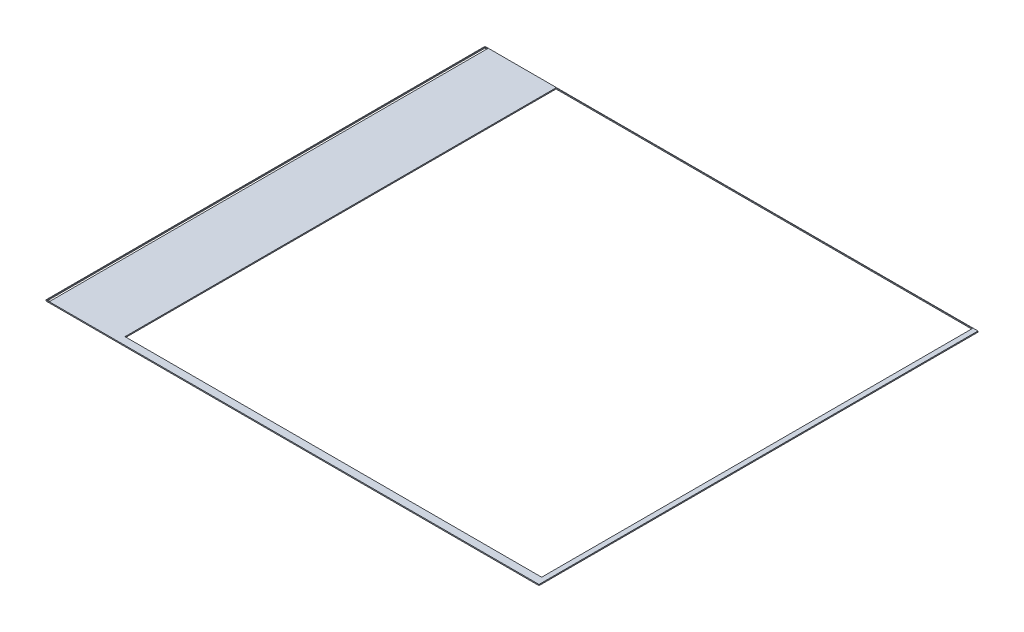
SolidWorks part; units mm, degrees
material "silicon D"
ref_plane "Front" through (0, 0, 0) normal (0, 0, 1) x (1, 0, 0)
ref_plane "Top" through (0, 0, 0) normal (0, 1, 0) x (1, 0, 0)
ref_plane "Right" through (0, 0, 0) normal (1, 0, 0) x (0, 0, -1)
sketch "Sketch1" plane through (0, 0, 0) normal (0, 1, 0) x (1, 0, 0)
  line L0 (11.355, 10.11) -> (-11.355, -10.11) construction
  line L1 (-11.355, 10.11) -> (11.355, 10.11) construction
  line L2 (-11.355, 10.11) -> (-11.355, -10.11) construction
  line L3 (-11.355, -10.11) -> (11.355, -10.11) construction
  line L4 (11.355, 10.11) -> (11.355, -10.11) construction
  line L5 (-11.365, 10.12) -> (11.365, 10.12)
  line L6 (11.365, 10.12) -> (11.365, -10.12)
  line L7 (-11.365, -10.12) -> (11.365, -10.12)
  line L8 (-11.365, 10.12) -> (-11.365, -10.12)
  point P4 (0, 0)
  dimension "D1" = 20.24
  dimension "D2" = 22.73
  dimension "D3" = 0.01
extrude "Extrude1" add sketch "Sketch1" along normal blind 0.05
sketch "Sketch2" plane through (0, 0, 0) normal (0, -1, 0) x (1, 0, 0)
  line L0 (-11.3446, 10.0882) -> (-11.2146, 10.0882) construction
  line L1 (-11.2146, -10.0968) -> (-11.3446, -10.0968) construction
  line L2 (-11.3446, -10.0968) -> (-11.3446, 10.0882) construction
  line L3 (-11.2146, 10.0882) -> (-11.2146, -10.0968) construction
  line L4 (-11.3446, 10.0882) -> (-11.2146, 10.0882)
  line L5 (-11.2146, -10.0968) -> (-11.3446, -10.0968)
  line L6 (-11.3446, -10.0968) -> (-11.3446, 10.0882)
  line L7 (-11.2146, 10.0882) -> (-11.2146, -10.0968)
extrude "Cut-Extrude1" cut sketch "Sketch2" against normal through all
sketch "Sketch3" plane through (0, 0, 0) normal (0, -1, 0) x (1, 0, 0)
  line L0 (-8.0718, 9.7706) -> (11.1378, 9.7706) construction
  line L1 (-8.0718, -10.1014) -> (-8.0718, 9.7706) construction
  line L2 (11.1378, 9.7706) -> (11.1378, -10.1014) construction
  line L3 (11.1378, -10.1014) -> (-8.0718, -10.1014) construction
  line L4 (-8.0718, 9.7706) -> (11.1378, 9.7706)
  line L5 (-8.0718, -10.1014) -> (-8.0718, 9.7706)
  line L6 (11.1378, 9.7706) -> (11.1378, -10.1014)
  line L7 (11.1378, -10.1014) -> (-8.0718, -10.1014)
extrude "Cut-Extrude2" cut sketch "Sketch3" against normal through all
